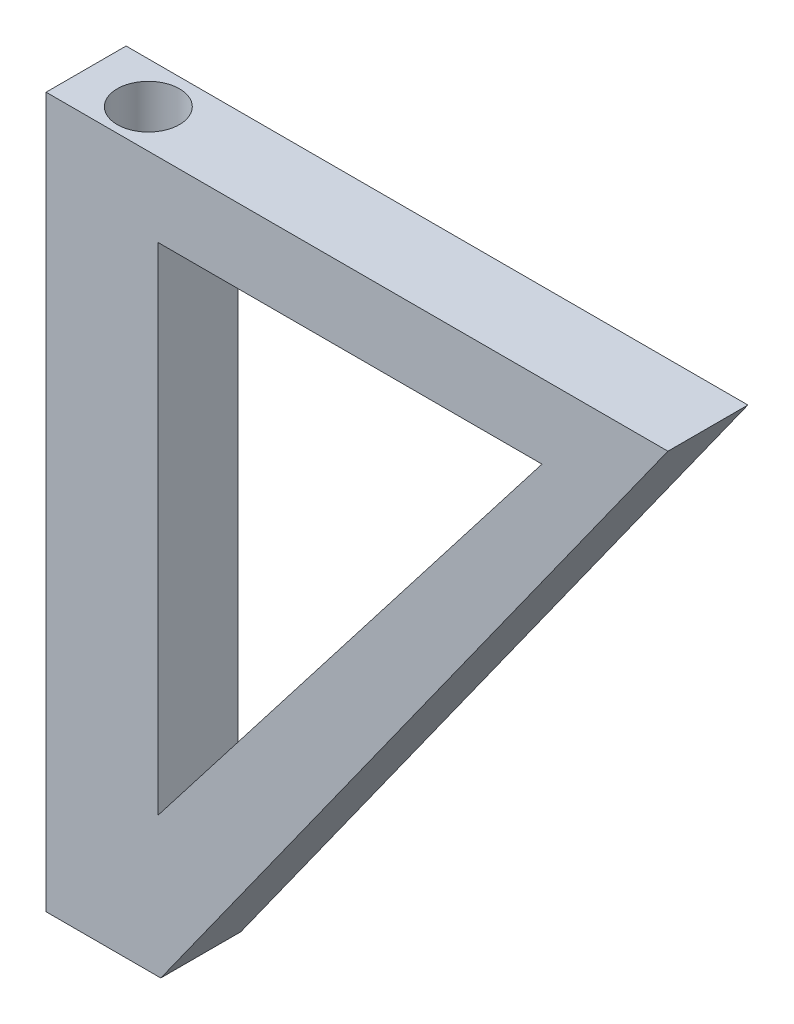
SolidWorks part; units mm, degrees
ref_plane "Plan de face" through (0, 0, 0) normal (0, 0, 1) x (1, 0, 0)
ref_plane "Plan de dessus" through (0, 0, 0) normal (0, 1, 0) x (1, 0, 0)
ref_plane "Plan de droite" through (0, 0, 0) normal (1, 0, 0) x (0, 0, -1)
sketch "Esquisse1" plane through (0, 0, 0) normal (0, 0, 1) x (1, 0, 0)
  line L0 (0, 0) -> (77.7382, 0)
  line L1 (77.7382, 0) -> (14.3371, -88.7375)
  line L2 (14.3371, -88.7375) -> (0, -88.7375)
  line L3 (0, -88.7375) -> (0, 0)
  point P3 (14.3371, -88.7375)
extrude "Boss.-Extru.1" add sketch "Esquisse1" along normal blind 10
sketch "Esquisse2" plane through (0, 0, 0) normal (0, 1, 0) x (1, 0, 0)
  circle A0 centre (7.9599, -5.1794) radius 3.8892
extrude "Enlèv. mat.-Extru.1" cut sketch "Esquisse2" against normal through all
sketch "Esquisse4" plane through (0, 0, 10) normal (0, 0, 1) x (1, 0, 0)
  line L0 (13.9926, -9.273) -> (13.9926, -71.2892)
  line L3 (13.9926, -71.2892) -> (61.9938, -9.273)
  line L4 (61.9938, -9.273) -> (13.9926, -9.273)
extrude "Enlèv. mat.-Extru.2" cut sketch "Esquisse4" against normal through all
